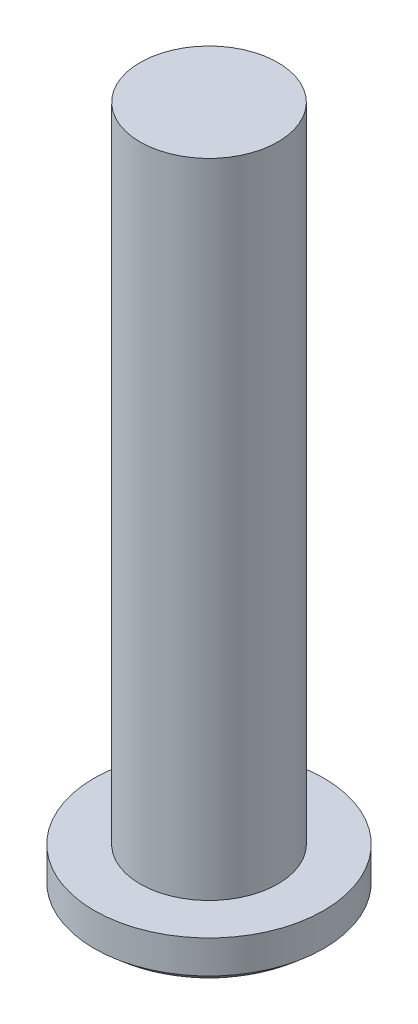
SolidWorks part; units mm, degrees
ref_plane "Front" through (0, 0, 0) normal (0, 0, 1) x (1, 0, 0)
ref_plane "Top" through (0, 0, 0) normal (0, 1, 0) x (1, 0, 0)
ref_plane "Right" through (0, 0, 0) normal (1, 0, 0) x (0, 0, -1)
sketch "草图1" plane through (0, 0, 0) normal (0, 1, 0) x (1, 0, 0)
  circle A0 centre (0, 0) radius 2.5
  dimension "D1" = 5
extrude "凸台-拉伸1" add sketch "草图1" along normal blind 1.7
sketch "草图2" plane through (0, 1.7, 0) normal (0, 1, 0) x (1, 0, 0)
  circle A0 centre (0, 0) radius 1.5
  dimension "D1" = 3
extrude "凸台-拉伸2" add sketch "草图2" along normal blind 14
sketch "草图3" plane through (0, 0, 0) normal (1, 0, 0) x (0, 0, -1)
  line L0 (-2.5, 0.9822) -> (-3.6323, -0.9364)
  line L2 (0, 1.0359) -> (0, -1.9035) construction
  line L3 (-3.6323, -0.9364) -> (3.5435, -0.9364)
  line L4 (3.5435, -0.9364) -> (2.5, 0.9822)
  line L5 (2.5, 0) -> (2.5, 1.7) construction
  line L6 (-2.5, 1.7) -> (-2.5, 0) construction
  arc A0 (-2.5, 0.9822) -> (2.5, 0.9822) centre (0, 3.6727) ccw
  point P1 (0, 3.6727)
revolve "切除-旋转3" cut sketch "草图3" angle 360 about L2
ref_plane "基准面1" through (0, -5, 0) normal (0, 1, 0) x (1, 0, 0)
sketch "草图4" plane through (0, -5, 0) normal (0, 1, 0) x (1, 0, 0)
  line L0 (-1, 0) -> (1, 0) construction
  line L1 (0, -1) -> (0, 1) construction
  line L2 (-1, -0.2) -> (-0.2, -0.2)
  line L3 (0.2, -1) -> (0.2, -0.2)
  line L4 (-1, 0.2) -> (-0.2, 0.2)
  line L5 (-0.2, -1) -> (-0.2, -0.2)
  line L6 (-1, -0.2) -> (-1, 0.2)
  line L7 (1, -0.2) -> (1, 0.2)
  line L8 (0.2, -1) -> (-0.2, -1)
  line L9 (0.2, 1) -> (-0.2, 1)
  line L10 (0.2, -0.2) -> (1, -0.2)
  line L11 (-0.2, 0.2) -> (-0.2, 1)
  line L12 (-1, -0.2) -> (1, -0.2) construction
  line L13 (0.2, 0.2) -> (1, 0.2)
  line L14 (-0.2, -1) -> (-0.2, 1) construction
  line L15 (0.2, 0.2) -> (0.2, 1)
  line L16 (-1, 0.2) -> (1, 0.2) construction
  line L18 (0.2, -1) -> (0.2, 1) construction
  dimension "D1" = 1
  dimension "D2" = 1
  dimension "D3" = 1
  dimension "D4" = 1
  dimension "D5" = 0.2
  dimension "D6" = 0.2
extrude "切除-拉伸1" cut sketch "草图4" along normal offset from surface (6.1 mm away) 0.6 up to face at (0, 1.7, 1.5)
